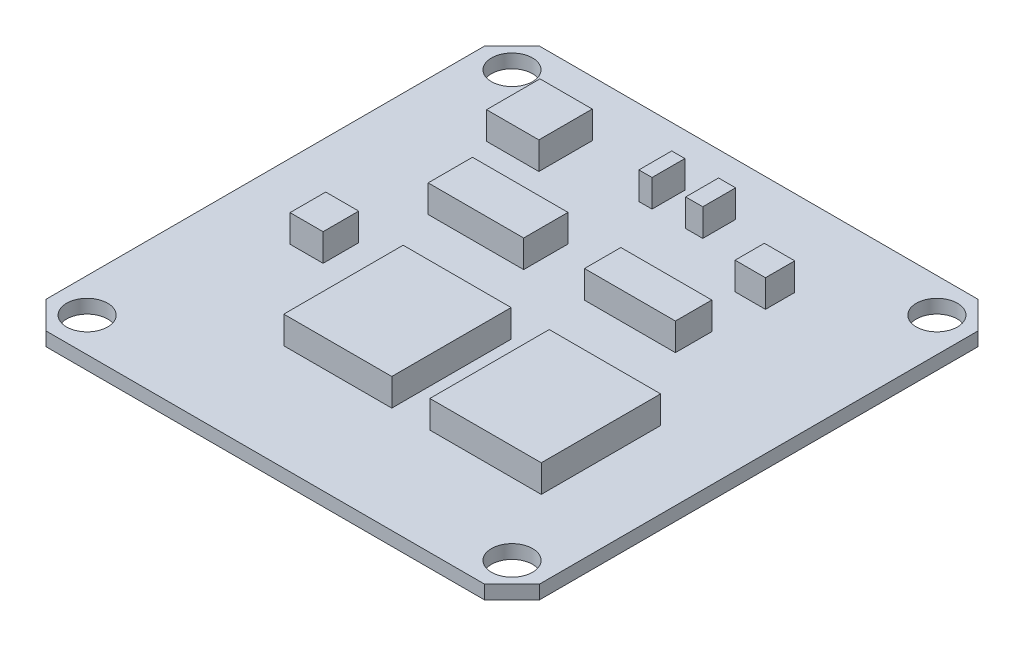
SolidWorks part; units mm, degrees
ref_plane "Front Plane" through (0, 0, 0) normal (0, 0, 1) x (1, 0, 0)
ref_plane "Top Plane" through (0, 0, 0) normal (0, 1, 0) x (1, 0, 0)
ref_plane "Right Plane" through (0, 0, 0) normal (1, 0, 0) x (0, 0, -1)
sketch "Sketch1" plane through (0, 0, 0) normal (0, 1, 0) x (1, 0, 0)
  line L1 (-18, 18) -> (18, 18)
  line L2 (-18, 18) -> (-18, -18)
  line L3 (-18, -18) -> (18, -18)
  line L4 (18, 18) -> (18, -18)
  line L5 (-18, 18) -> (18, -18) construction
  line L6 (-18, -18) -> (18, 18) construction
  point P0 (0, 0)
  dimension "D1" = 36
  dimension "D2" = 36
extrude "Boss-Extrude1" add sketch "Sketch1" along normal blind 1
sketch "Sketch2" plane through (0, 1, 0) normal (0, 1, 0) x (1, 0, 0)
  line L0 (-18, 18) -> (-18, -18) construction
  line L1 (-11.9077, 13.9491) -> (-8.0923, 13.9491)
  line L2 (-11.9077, 13.9491) -> (-11.9077, 10.0509)
  line L3 (-11.9077, 10.0509) -> (-8.0923, 10.0509)
  line L4 (-8.0923, 13.9491) -> (-8.0923, 10.0509)
  line L5 (-11.9077, 13.9491) -> (-8.0923, 10.0509) construction
  line L6 (-11.9077, 10.0509) -> (-8.0923, 13.9491) construction
  line L7 (-6.3865, -1.5552) -> (1.493, -1.5552)
  line L8 (-6.3865, -1.5552) -> (-6.3865, -10.2641)
  line L9 (-6.3865, -10.2641) -> (1.493, -10.2641)
  line L10 (1.493, -1.5552) -> (1.493, -10.2641)
  line L11 (-6.3865, -1.5552) -> (1.493, -10.2641) construction
  line L12 (-6.3865, -10.2641) -> (1.493, -1.5552) construction
  line L13 (4.2715, -1.5552) -> (12.3999, -1.5552)
  line L14 (4.2715, -1.5552) -> (4.2715, -10.2641)
  line L15 (4.2715, -10.2641) -> (12.3999, -10.2641)
  line L16 (12.3999, -1.5552) -> (12.3999, -10.2641)
  line L17 (4.2715, -1.5552) -> (12.3999, -10.2641) construction
  line L18 (4.2715, -10.2641) -> (12.3999, -1.5552) construction
  line L19 (1.7003, 6.2414) -> (8.3357, 6.2414)
  line L20 (1.7003, 6.2414) -> (1.7003, 3.5872)
  line L21 (1.7003, 3.5872) -> (8.3357, 3.5872)
  line L22 (8.3357, 6.2414) -> (8.3357, 3.5872)
  line L23 (1.7003, 6.2414) -> (8.3357, 3.5872) construction
  line L24 (1.7003, 3.5872) -> (8.3357, 6.2414) construction
  line L25 (-9.4139, 6.5317) -> (-2.4468, 6.5317)
  line L26 (-9.4139, 6.5317) -> (-9.4139, 3.297)
  line L27 (-9.4139, 3.297) -> (-2.4468, 3.297)
  line L28 (-2.4468, 6.5317) -> (-2.4468, 3.297)
  line L29 (-9.4139, 6.5317) -> (-2.4468, 3.297) construction
  line L30 (-9.4139, 3.297) -> (-2.4468, 6.5317) construction
  line L31 (-2.5446, 14.1996) -> (-1.5859, 14.1996)
  line L32 (-2.5446, 14.1996) -> (-2.5446, 11.8028)
  line L33 (-2.5446, 11.8028) -> (-1.5859, 11.8028)
  line L34 (-1.5859, 14.1996) -> (-1.5859, 11.8028)
  line L35 (-2.5446, 14.1996) -> (-1.5859, 11.8028) construction
  line L36 (-2.5446, 11.8028) -> (-1.5859, 14.1996) construction
  line L37 (0.8709, 14.1996) -> (2.115, 14.1996)
  line L38 (0.8709, 14.1996) -> (0.8709, 11.8028)
  line L39 (0.8709, 11.8028) -> (2.115, 11.8028)
  line L40 (2.115, 14.1996) -> (2.115, 11.8028)
  line L41 (0.8709, 14.1996) -> (2.115, 11.8028) construction
  line L42 (0.8709, 11.8028) -> (2.115, 14.1996) construction
  line L43 (18, 18) -> (-18, 18) construction
  point P0 (-10, 12)
  point P5 (-2.4468, -5.9096)
  point P10 (8.3357, -5.9096)
  point P15 (5.018, 4.9143)
  point P20 (-5.9304, 4.9143)
  point P25 (-2.0653, 13.0012)
  point P30 (1.493, 13.0012)
  dimension "D1" = 8
  dimension "D2" = 6
extrude "Boss-Extrude2" add sketch "Sketch2" along normal blind 2
chamfer "Chamfer1" distance 2 angle 45 4 edges at (18, 0.5, -18) (18, 0.5, 18) (-18, 0.5, 18) (-18, 0.5, -18)
sketch "Sketch3" plane through (0, 1, 0) normal (0, 1, 0) x (1, 0, 0)
  line L1 (-12.5717, -1.0201) -> (-10.1631, -1.0201)
  line L2 (-12.5717, -1.0201) -> (-12.5717, -3.6213)
  line L3 (-12.5717, -3.6213) -> (-10.1631, -3.6213)
  line L4 (-10.1631, -1.0201) -> (-10.1631, -3.6213)
  line L5 (-12.5717, -1.0201) -> (-10.1631, -3.6213) construction
  line L6 (-12.5717, -3.6213) -> (-10.1631, -1.0201) construction
  line L7 (6.668, 11.7443) -> (8.8855, 11.7443)
  line L8 (6.668, 11.7443) -> (6.668, 9.607)
  line L9 (6.668, 9.607) -> (8.8855, 9.607)
  line L10 (8.8855, 11.7443) -> (8.8855, 9.607)
  line L11 (6.668, 11.7443) -> (8.8855, 9.607) construction
  line L12 (6.668, 9.607) -> (8.8855, 11.7443) construction
  point P0 (-11.3674, -2.3207)
  point P5 (7.7767, 10.6757)
extrude "Boss-Extrude3" add sketch "Sketch3" along normal blind 2
sketch "Sketch4" plane through (0, 1, 0) normal (0, 1, 0) x (1, 0, 0)
  line L0 (16, 18) -> (-16, 18) construction
  line L1 (-18, 16) -> (-18, -16) construction
  circle A0 centre (-15.5, 15.5) radius 1.5
  dimension "D1" = 2.5
  dimension "D3" = 3
  dimension "D2" = 2.5
extrude "Cut-Extrude1" cut sketch "Sketch4" against normal through all
pattern_linear "LPattern1" count 2 spacing 31 along (1, 0, 0) count 2 spacing 31 along (0, 0, 1) of "Cut-Extrude1"
